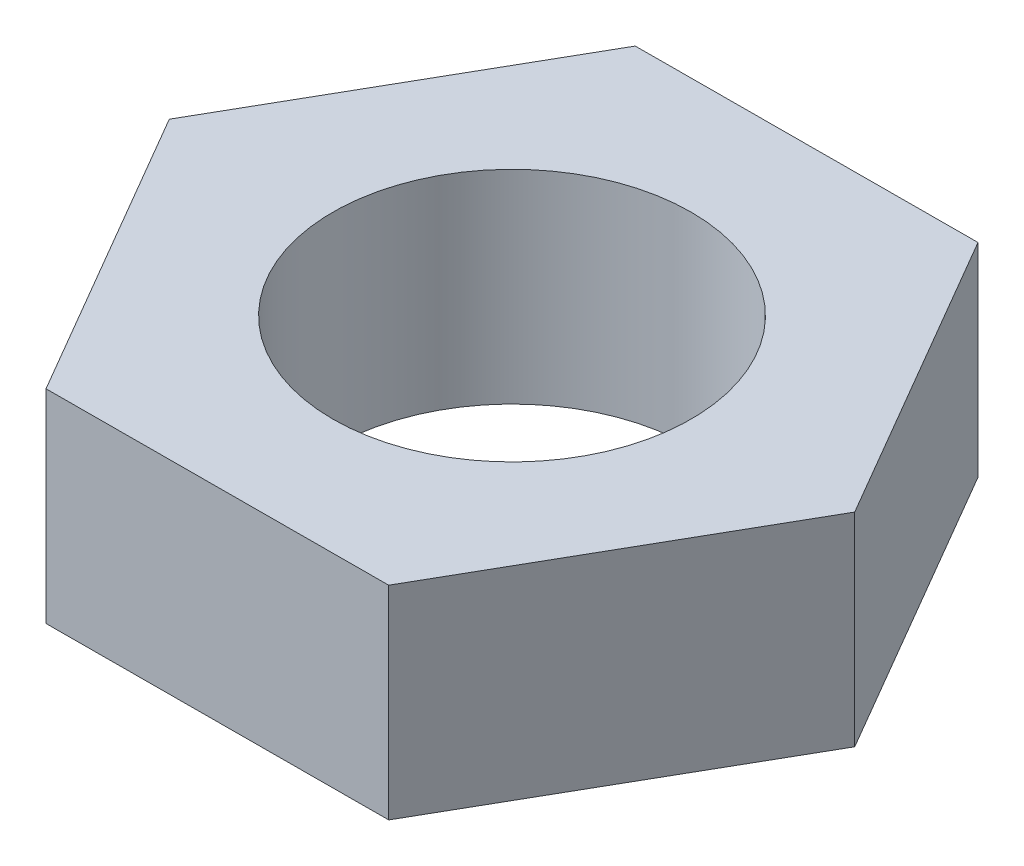
SolidWorks part; units mm, degrees
ref_plane "Front Plane" through (0, 0, 0) normal (0, 0, 1) x (1, 0, 0)
ref_plane "Top Plane" through (0, 0, 0) normal (0, 1, 0) x (1, 0, 0)
ref_plane "Right Plane" through (0, 0, 0) normal (1, 0, 0) x (0, 0, -1)
sketch "Sketch1" plane through (0, 0, 0) normal (0, 1, 0) x (1, 0, 0)
  line L1 (7.6938, 13.4395) -> (-7.792, 13.3828)
  line L2 (-7.792, 13.3828) -> (-15.4858, -0.0567)
  line L3 (-15.4858, -0.0567) -> (-7.6938, -13.4395)
  line L4 (-7.6938, -13.4395) -> (7.792, -13.3828)
  line L5 (7.792, -13.3828) -> (15.4858, 0.0567)
  line L6 (15.4858, 0.0567) -> (7.6938, 13.4395)
  circle A0 centre (0, 0) radius 13.4112 construction
  dimension "D1" = 26.8224
extrude "Boss-Extrude1" add sketch "Sketch1" along normal blind 9.22 contours L1 L2 L3 L4 L5 L6
sketch "Sketch2" plane through (0, 9.22, 0) normal (0, 1, 0) x (1, 0, 0)
  circle A0 centre (0, 0) radius 8.128
extrude "Cut-Extrude1" cut sketch "Sketch2" against normal through all
